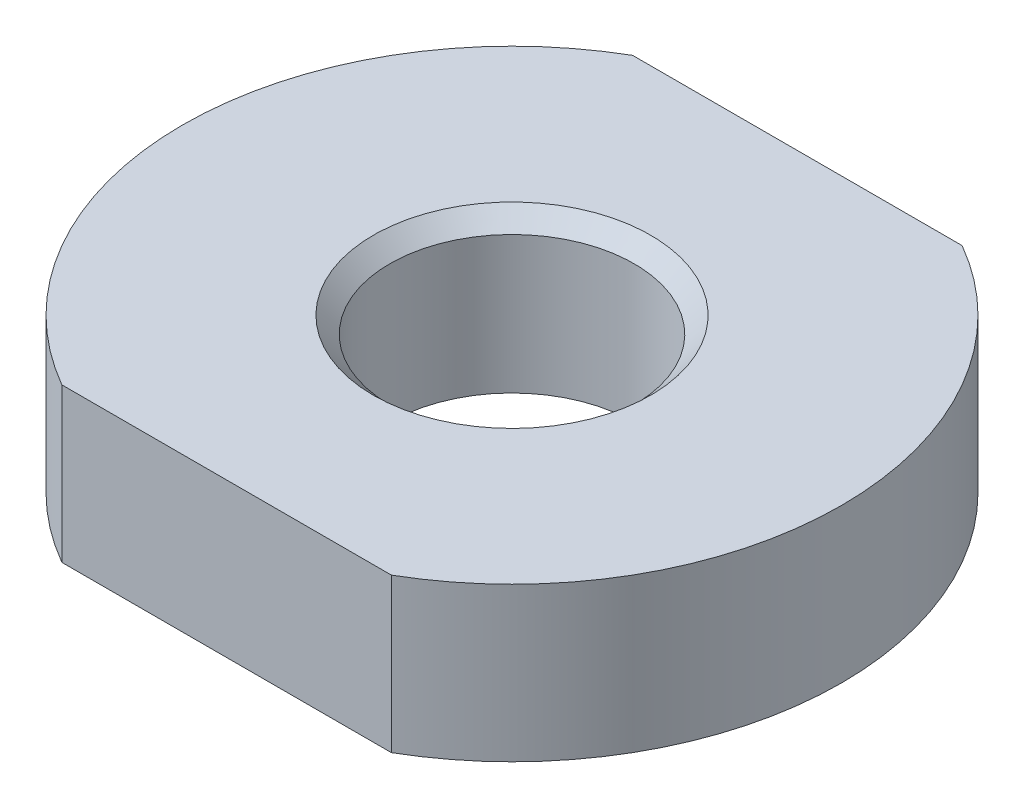
SolidWorks part; units mm, degrees
ref_plane "Front Plane" through (0, 0, 0) normal (0, 0, 1) x (1, 0, 0)
ref_plane "Top Plane" through (0, 0, 0) normal (0, 1, 0) x (1, 0, 0)
ref_plane "Right Plane" through (0, 0, 0) normal (1, 0, 0) x (0, 0, -1)
sketch "Sketch1" plane through (0, 0, 0) normal (0, 1, 0) x (1, 0, 0)
  line L0 (-1000, 0) -> (49000, 0) construction
  line L1 (6, 10.3923) -> (-6, 10.3923)
  line L2 (6, -10.3923) -> (-6, -10.3923)
  circle A0 centre (0, 0) radius 4.45
  arc A1 (-6, 10.3923) -> (-6, -10.3923) centre (0, 0) ccw
  arc A2 (6, -10.3923) -> (6, 10.3923) centre (0, 0) ccw
  dimension "D1" = 8.9
  dimension "D2" = 24
  dimension "D3" = 12
extrude "Boss-Extrude1" add sketch "Sketch1" along normal blind 5.6
chamfer "Chamfer1" distance 0.6 1 edges at (0, 5.6, 4.45)
